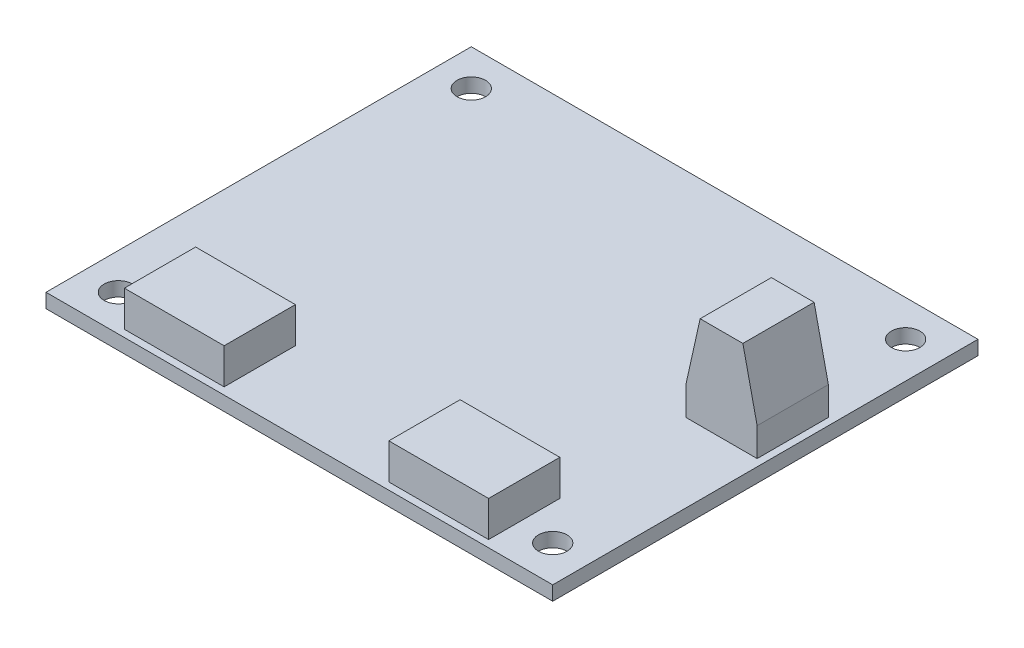
SolidWorks part; units mm, degrees
material "Silicon"
ref_plane "Front Plane" through (0, 0, 0) normal (0, 0, 1) x (1, 0, 0)
ref_plane "Top Plane" through (0, 0, 0) normal (0, 1, 0) x (1, 0, 0)
ref_plane "Right Plane" through (0, 0, 0) normal (1, 0, 0) x (0, 0, -1)
sketch "Sketch1" plane through (0, 0, 0) normal (0, 1, 0) x (1, 0, 0)
  line L0 (0, -29.845) -> (0, 29.845) construction
  line L1 (-35.56, 29.845) -> (35.56, 29.845)
  line L2 (-35.56, 29.845) -> (-35.56, -29.845)
  line L3 (-35.56, -29.845) -> (35.56, -29.845)
  line L4 (35.56, 29.845) -> (35.56, -29.845)
  dimension "D1" = 71.12
  dimension "D2" = 59.69
extrude "Boss-Extrude1" add sketch "Sketch1" along normal blind 2
sketch "Sketch2" plane through (0, 2, 0) normal (0, 1, 0) x (1, 0, 0)
  line L1 (-30.48, 24.765) -> (30.48, 24.765) construction
  line L2 (0, 0) -> (-35.56, 0) construction
  line L3 (30.48, -24.765) -> (0, -24.765) construction
  line L4 (30.48, 24.765) -> (30.48, -24.765) construction
  line L6 (0, -29.845) -> (0, 0) construction
  line L7 (-35.56, -29.845) -> (35.56, -29.845) construction
  line L8 (0, -24.765) -> (-30.48, -24.765) construction
  line L9 (-35.56, 29.845) -> (-35.56, -29.845) construction
  line L10 (-30.48, 24.765) -> (-30.48, 0) construction
  line L11 (-30.48, 0) -> (-30.48, -24.765) construction
  circle A0 centre (-30.48, 24.765) radius 2
  circle A1 centre (30.48, 24.765) radius 2
  circle A2 centre (30.48, -24.765) radius 2
  circle A3 centre (-30.48, -24.765) radius 2
  dimension "D5" = 4
  dimension "D3" = 60.96
  dimension "D4" = 49.53
extrude "Cut-Extrude1" cut sketch "Sketch2" against normal blind 2
sketch "Sketch3" plane through (0, 2, 0) normal (0, 1, 0) x (1, 0, 0)
  line L0 (0, -29.845) -> (0, 29.845) construction
  line L1 (-11.56, -28.845) -> (-25.56, -28.845)
  line L2 (-11.56, -28.845) -> (-11.56, -18.845)
  line L3 (-11.56, -18.845) -> (-25.56, -18.845)
  line L4 (-25.56, -28.845) -> (-25.56, -18.845)
  line L5 (-35.56, -29.845) -> (35.56, -29.845) construction
  line L6 (35.56, 29.845) -> (-35.56, 29.845) construction
  line L7 (11.56, -28.845) -> (25.56, -28.845)
  line L8 (25.56, -28.845) -> (25.56, -18.845)
  line L9 (11.56, -28.845) -> (11.56, -18.845)
  line L10 (11.56, -18.845) -> (25.56, -18.845)
  line L11 (-35.56, 29.845) -> (-35.56, -29.845) construction
  dimension "D1" = 14
  dimension "D2" = 10
  dimension "D3" = 10
  dimension "D4" = 1
extrude "Boss-Extrude2" add sketch "Sketch3" along normal blind 5
sketch "Sketch4" plane through (0, 2, 0) normal (0, 1, 0) x (1, 0, 0)
  line L0 (35.56, 29.845) -> (-35.56, 29.845) construction
  line L1 (24.56, 9.845) -> (34.56, 9.845)
  line L2 (24.56, 9.845) -> (24.56, -0.155)
  line L3 (24.56, -0.155) -> (34.56, -0.155)
  line L4 (34.56, 9.845) -> (34.56, -0.155)
  line L5 (35.56, -29.845) -> (35.56, 29.845) construction
  dimension "D1" = 20
  dimension "D2" = 1
  dimension "D3" = 10
extrude "Boss-Extrude3" add sketch "Sketch4" along normal blind 13
sketch "Sketch7" plane through (0, 0, 0.155) normal (0, 0, 1) x (1, 0, 0)
  line L0 (26.56, 15) -> (24.56, 6)
  line L1 (24.56, 15) -> (34.56, 15) construction
  line L3 (24.56, 15) -> (24.56, 2) construction
  line L4 (24.56, 6) -> (34.56, 6) construction
  line L5 (34.56, 15) -> (34.56, 2) construction
  line L6 (34.56, 6) -> (32.56, 15)
  line L7 (32.56, 15) -> (26.56, 15) construction
  line L8 (24.56, 2) -> (34.56, 2) construction
  line L9 (34.56, 6) -> (34.56, 15)
  line L10 (34.56, 15) -> (32.56, 15)
  line L11 (26.56, 15) -> (24.56, 15)
  line L12 (24.56, 15) -> (24.56, 6)
  dimension "D1" = 6
  dimension "D2" = 4
extrude "Cut-Extrude2" cut sketch "Sketch7" against normal through all
